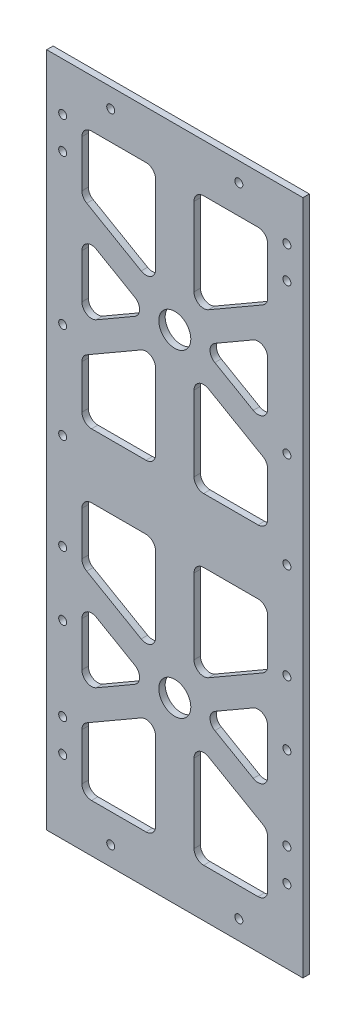
SolidWorks part; units mm, degrees
material "6061-T6 (SS)"
ref_plane "Front Plane" through (0, 0, 0) normal (0, 0, 1) x (1, 0, 0)
ref_plane "Top Plane" through (0, 0, 0) normal (0, 1, 0) x (1, 0, 0)
ref_plane "Right Plane" through (0, 0, 0) normal (1, 0, 0) x (0, 0, -1)
sketch "Sketch1" plane through (0, 0, 0) normal (0, 0, 1) x (1, 0, 0)
  line L1 (0, 0) -> (88, 0)
  line L2 (0, 0) -> (0, 211)
  line L3 (0, 211) -> (88, 211)
  line L4 (88, 0) -> (88, 211)
  dimension "D1" = 88
  dimension "D2" = 211
extrude "Boss-Extrude1" add sketch "Sketch1" along normal blind 2
sketch "Sketch2" plane through (0, 0, 2) normal (0, 0, 1) x (1, 0, 0)
  line L0 (0, 105.5) -> (88, 105.5) construction
  line L1 (0, 211) -> (0, 0) construction
  line L2 (88, 0) -> (88, 211) construction
  line L3 (44, 211) -> (44, 0) construction
  line L4 (88, 211) -> (0, 211) construction
  line L5 (0, 0) -> (88, 0) construction
  line L6 (0, 155.25) -> (88, 155.25) construction
  line L7 (0, 55.75) -> (88, 55.75) construction
  dimension "D1" = 55.75
  dimension "D2" = 55.75
sketch "Sketch3" plane through (0, 0, 2) normal (0, 0, 1) x (1, 0, 0)
  line L0 (0, 155.25) -> (88, 155.25) construction
  line L1 (38, 196) -> (38, 115.5)
  line L2 (0, 211) -> (0, 0) construction
  line L3 (15, 196) -> (73, 196)
  line L4 (15, 196) -> (15, 115.5)
  line L5 (15, 115.5) -> (73, 115.5)
  line L6 (73, 196) -> (73, 115.5)
  line L7 (88, 211) -> (0, 211) construction
  line L8 (88, 0) -> (88, 211) construction
  line L9 (0, 105.5) -> (88, 105.5) construction
  line L13 (73, 171.9932) -> (15, 138.5068) construction
  line L14 (15, 171.9932) -> (73, 138.5068) construction
  line L15 (73, 176.612) -> (15, 143.1256)
  line L16 (73, 167.3744) -> (15, 133.888)
  line L17 (15, 176.612) -> (73, 143.1256)
  line L18 (15, 167.3744) -> (73, 133.888)
  line L19 (50, 196) -> (50, 115.5)
  circle A0 centre (44, 155.25) radius 5
  dimension "D1" = 10
  dimension "D3" = 15
  dimension "D4" = 15
  dimension "D5" = 15
  dimension "D6" = 10
  dimension "D9" = 30
  dimension "D10" = 30
  dimension "D11" = 8
  dimension "D12" = 4
  dimension "D13" = 4
  dimension "D14" = 8
ref_plane "Plane1" through (0, 105.5, 0) normal (0, 1, 0) x (1, 0, 0)
extrude "Cut-Extrude2" cut sketch "Sketch3" against normal blind 2
sketch "Sketch4" plane through (0, 0, 2) normal (0, 0, 1) x (1, 0, 0)
  line L0 (0, 155.25) -> (88, 155.25) construction
  circle A0 centre (44, 155.25) radius 5
  dimension "D1" = 10
extrude "Cut-Extrude3" cut sketch "Sketch4" against normal through all
mirror "Mirror2" about plane through (0, 105.5, 0) normal (0, 1, 0) of "Cut-Extrude2", "Cut-Extrude3"
fillet "Fillet2" radius 3 44 edges at (73, 67.8744, 1) (73, 43.6256, 1) (52, 55.75, 1) (15, 15, 1) (15, 34.388, 1) (15, 143.1256, 1) (15, 167.3744, 1) (36, 155.25, 1) (15, 115.5, 1) (15, 133.888, 1) (73, 196, 1) (73, 115.5, 1) (73, 133.888, 1) (15, 196, 1) (15, 176.612, 1) (73, 167.3744, 1) (73, 143.1256, 1) (52, 155.25, 1) (73, 95.5, 1) (73, 77.112, 1) (73, 34.388, 1) (73, 15, 1) (15, 77.112, 1) (15, 95.5, 1) (15, 43.6256, 1) (15, 67.8744, 1) (36, 55.75, 1) (73, 176.612, 1) (50, 15, 1) (38, 15, 1) (38, 47.6671, 1) (50, 47.6671, 1) (38, 63.8329, 1) (38, 95.5, 1) (50, 63.8329, 1) (50, 95.5, 1) (38, 115.5, 1) (38, 147.1671, 1) (50, 147.1671, 1) (50, 115.5, 1) (38, 196, 1) (38, 163.3329, 1) (50, 163.3329, 1) (50, 196, 1)
sketch "Sketch23" plane through (0, 0, 2) normal (0, 0, 1) x (1, 0, 0)
  line L2 (88, 211) -> (88, 0)
  line L3 (86, 211) -> (86, 0)
  line L4 (86, 211) -> (88, 211)
  line L5 (86, 0) -> (88, 0)
  line L6 (2.1504, 211) -> (2.1504, 0)
  line L7 (2.1504, 211) -> (0, 211)
  line L8 (0, 211) -> (0, 0)
  line L9 (2.1504, 0) -> (0, 0)
  dimension "D1" = 2
extrude "Cut-Extrude5" cut sketch "Sketch23" against normal blind 10 contours L5 L2 L4 L3 | L6 L9 L8 L7
sketch "Sketch29" plane through (0, 0, 0) normal (0, 0, -1) x (-1, 0, 0)
  line L0 (-44, 0) -> (-44, 211)
  line L4 (-86, 105.5) -> (-2.1504, 105.5)
  line L5 (-86, 0) -> (-86, 211) construction
  line L6 (-2.1504, 0) -> (-2.1504, 211) construction
  line L16 (-4, 211) -> (1.9115, 211)
  line L17 (-4, 211) -> (-4, 0)
  line L18 (-4, 0) -> (1.9115, 0)
  line L19 (1.9115, 211) -> (1.9115, 0)
  line L20 (-84, 0) -> (-88.0365, 0)
  line L21 (-84, 0) -> (-84, 211)
  line L22 (-84, 211) -> (-88.0365, 211)
  line L23 (-88.0365, 0) -> (-88.0365, 211)
  point P0 (-44, 155.25)
  point P1 (-44, 217.1483)
  point P3 (-4, 155.25)
  point P4 (-4, 217.1483)
  point P5 (-84, 155.25)
  point P6 (-84, 217.1483)
  point P8 (-4, 105.5)
  point P22 (-84, 105.5)
  point P23 (-44, 105.5)
extrude "Cut-Extrude10" cut sketch "Sketch29" against normal blind 2
hole_wizard "M3x0.5 Tapped Hole1" positions "Sketch31" profile "Sketch32" tap size "M3x0.5" standard "ANSI Metric"
sketch "Sketch31" plane through (0, 0, 2) normal (0, 0, 1) x (1, 0, 0)
  line L0 (44, 211) -> (44, 0) construction
  line L1 (84, 211) -> (4, 211) construction
  line L2 (4, 0) -> (84, 0) construction
  line L3 (9, 186) -> (44, 211) construction
  line L4 (44, 211) -> (79, 186) construction
  line L5 (4, 0) -> (84, 0) construction
  line L6 (84, 211) -> (4, 211) construction
  point P0 (9, 186)
  point P2 (9, 139.2)
  point P4 (9, 109.2)
  point P6 (9, 79.2)
  point P8 (9, 59.2)
  point P10 (9, 33.2)
  point P20 (79, 186)
  point P22 (79, 139.2)
  point P24 (79, 109.2)
  point P26 (79, 79.2)
  point P28 (79, 59.2)
  point P30 (79, 33.2)
  point P51 (24, 6)
  point P53 (64, 6)
  point P59 (24, 205)
  point P61 (64, 205)
  point P70 (9, 196)
  point P72 (79, 196)
  point P76 (9, 23)
  point P78 (79, 23)
  dimension "D1" = 70
  dimension "D2" = 25
  dimension "D3" = 46.8
  dimension "D4" = 30
  dimension "D5" = 30
  dimension "D6" = 26
  dimension "D7" = 20
  dimension "D8" = 6
  dimension "D9" = 40
  dimension "D10" = 20
  dimension "D11" = 6
  dimension "D12" = 15
  dimension "D13" = 70
  dimension "D14" = 35
  dimension "D15" = 23
sketch "Sketch32" plane through (9, 186, 2) normal (1, 0, 0) x (0, -1, 0)
  line L0 (0, 0) -> (0, 10.7511)
  line L1 (0, 10.7511) -> (1.25, 10)
  line L2 (1.25, 10) -> (1.25, 0)
  line L5 (1.25, 0) -> (0, 0)
  line L10 (0, 10.7511) -> (-1.25, 10) construction
  line L11 (0, -6.35) -> (0, 107.95) construction
  dimension "Tap Drill Dia." = 2.5
  dimension "Tap Drill Depth" = 10
  dimension "Drill Angle" = 118
equation "\"stack_house_hole_distance\"=15"
equation "\"battery_top_clearance\"=15"
equation "\"coils_top_clearance\"=10"
